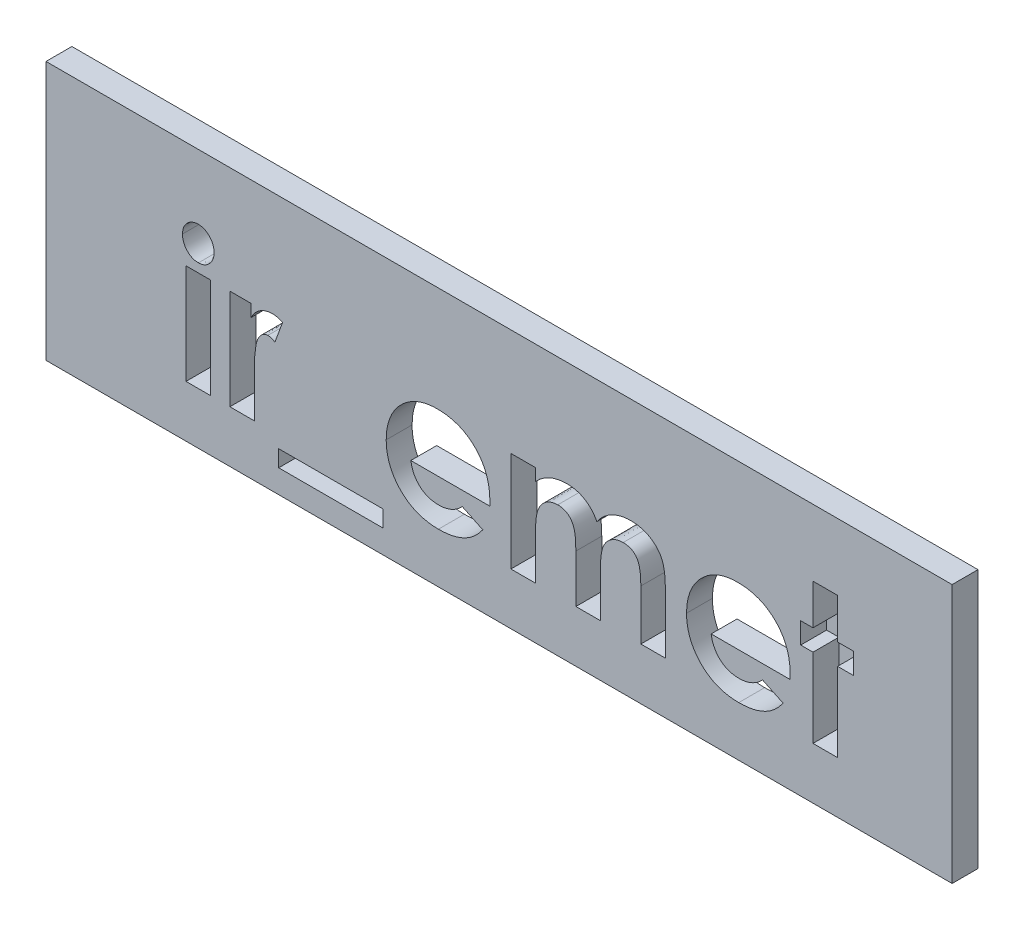
SolidWorks part; units mm, degrees
ref_plane "Plan de face" through (0, 0, 0) normal (0, 0, 1) x (1, 0, 0)
ref_plane "Plan de dessus" through (0, 0, 0) normal (0, 1, 0) x (1, 0, 0)
ref_plane "Plan de droite" through (0, 0, 0) normal (1, 0, 0) x (0, 0, -1)
sketch "Esquisse1" plane through (0, 0, 0) normal (0, 0, 1) x (1, 0, 0)
  line L1 (0, 0) -> (35, 0)
  line L2 (0, 0) -> (0, -10)
  line L3 (0, -10) -> (35, -10)
  line L4 (35, 0) -> (35, -10)
  dimension "D1" = 35
  dimension "D2" = 10
extrude "Boss.-Extru.1" add sketch "Esquisse1" along normal blind 1
sketch "Esquisse2" plane through (0, 0, 0) normal (0, 0, -1) x (-1, 0, 0)
  line L0 (-35, 0) -> (0, 0) construction
  line L1 (-35, -10) -> (-35, 0) construction
  line L2 (0, 0) -> (0, -10) construction
  circle A0 centre (-30, -5) radius 1
  circle A1 centre (-5, -5) radius 1
  dimension "D4" = 2
  dimension "D1" = 5
  dimension "D2" = 5
  dimension "D3" = 5
extrude "Boss.-Extru.2" add sketch "Esquisse2" along normal blind 3
chamfer "Chanfrein1" distance 0.5 angle 45 2 edges at (29, -5, -3) (4, -5, -3)
sketch "Esquisse3" plane through (0, 0, 1) normal (0, 0, 1) x (1, 0, 0)
  line L0 (5, -8) -> (30, -8) construction
  line L3 (0, -10) -> (35, -10) construction
  line L4 (0, 0) -> (0, -10) construction
  line L5 (35, -10) -> (35, 0) construction
  text T1 "<b>ir_emet</b>" font "Century Gothic" height in points 20
  point P12 (30, -8)
  dimension "D1" = 2
  dimension "D2" = 5
  dimension "D3" = 25
  dimension "D4" = 5
extrude "Enlèv. mat.-Extru.2" cut sketch "Esquisse3" against normal blind 1
sketch "Esquisse4" plane through (0, 0, 1) normal (0, 0, 1) x (1, 0, 0)
  line L8 (8.9884, -9.0998) -> (13.0197, -9.0998)
  line L9 (8.9884, -8.4606) -> (8.9884, -9.0998)
  line L10 (13.0197, -8.4606) -> (8.9884, -8.4606)
  line L11 (13.0197, -9.0998) -> (13.0197, -8.4606)
  line L12 (8.9884, -9.0998) -> (13.0197, -9.0998)
  line L13 (8.9884, -8.4606) -> (8.9884, -9.0998)
  line L14 (13.0197, -8.4606) -> (8.9884, -8.4606)
  line L15 (13.0197, -9.0998) -> (13.0197, -8.4606)
  dimension "D1" = 0.15
extrude "Enlèv. mat.-Extru.3" cut sketch "Esquisse4" against normal through all
